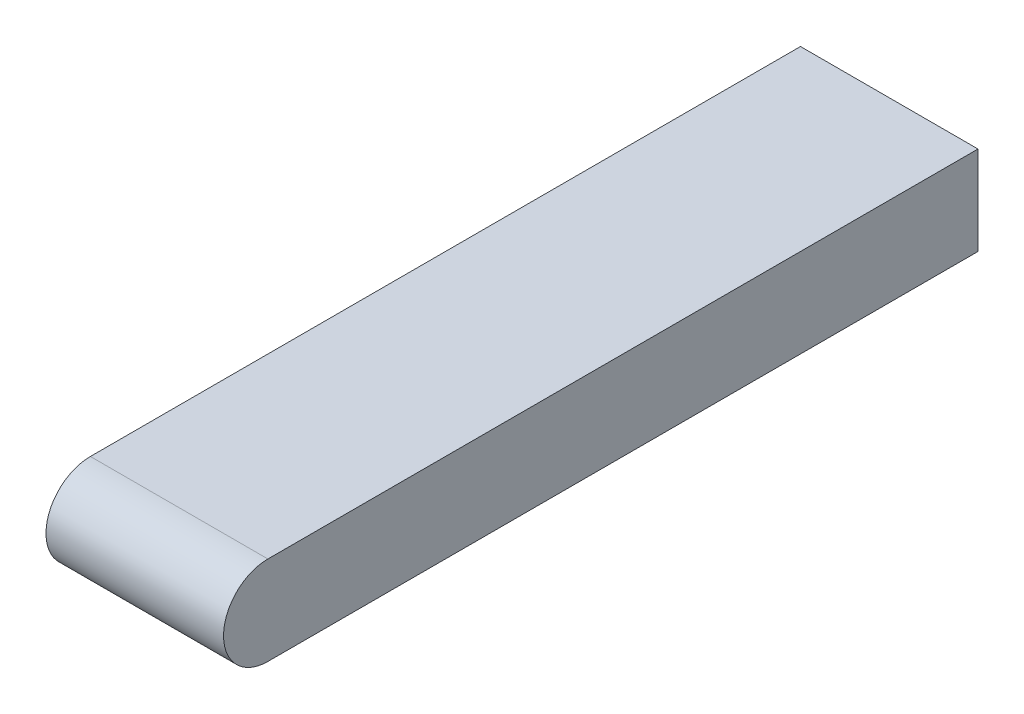
SolidWorks part; units mm, degrees
ref_plane "Front Plane" through (0, 0, 0) normal (0, 0, 1) x (1, 0, 0)
ref_plane "Top Plane" through (0, 0, 0) normal (0, 1, 0) x (1, 0, 0)
ref_plane "Right Plane" through (0, 0, 0) normal (1, 0, 0) x (0, 0, -1)
sketch "Sketch1" plane through (0, 0, 0) normal (1, 0, 0) x (0, 0, -1)
  line L0 (0, 0) -> (88.9, 0) construction
  line L1 (0, -6.35) -> (88.9, -6.35)
  line L2 (0, 6.35) -> (88.9, 6.35)
  line L3 (88.9, 6.35) -> (88.9, -6.35)
  line L4 (0, 0) -> (-12.7, 0) construction
  line L5 (0, 6.35) -> (-12.7, 6.35)
  line L6 (0, -6.35) -> (-12.7, -6.35)
  arc A3 (-12.7, 6.35) -> (-12.7, -6.35) centre (-12.7, 0) ccw
  dimension "D7" = 101.6
  dimension "D1" = 88.9
  dimension "D5" = 12.7
  dimension "D2" = 6.35
  dimension "D3" = 6.35
extrude "Boss-Extrude1" add sketch "Sketch1" along normal blind 25.4
